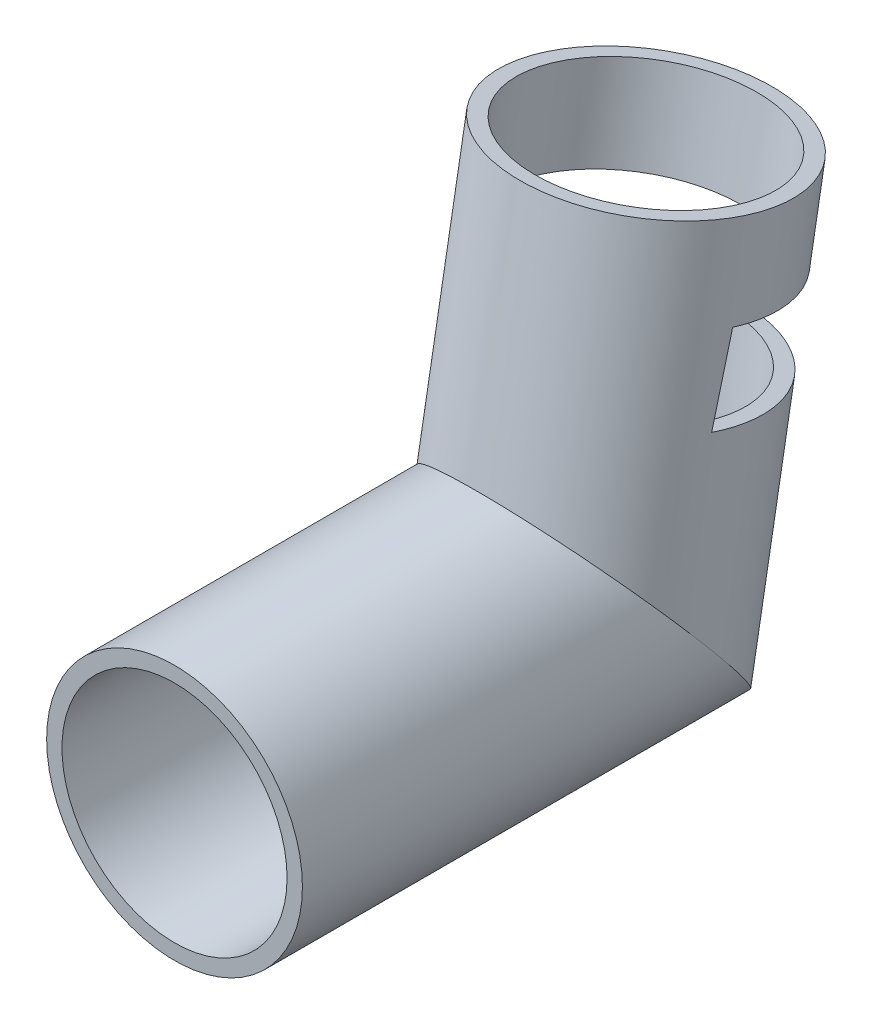
SolidWorks part; units mm, degrees
ref_plane "Front Plane" through (0, 0, 0) normal (0, 0, 1) x (1, 0, 0)
ref_plane "Top Plane" through (0, 0, 0) normal (0, 1, 0) x (1, 0, 0)
ref_plane "Right Plane" through (0, 0, 0) normal (1, 0, 0) x (0, 0, -1)
sketch "Sketch1" plane through (0, 0, 0) normal (1, 0, 0) x (0, 0, -1)
  line L0 (0, 0) -> (80, 0)
  line L1 (80, 0) -> (92.1554, 68.9365)
  line L2 (80, 0) -> (47.2364, 0) construction
  dimension "D1" = 80
sketch "Sketch3" plane through (0, 0, 0) normal (0, 0, 1) x (1, 0, 0)
  circle A0 centre (0, 0) radius 22
  circle A1 centre (0, 0) radius 25
sweep "Sweep1" add profiles "Sketch3" path "Sketch1"
sketch "Sketch4" plane through (0, 0, 0) normal (1, 0, 0) x (0, 0, -1)
  line L0 (80.6522, 36.2695) -> (50.0664, 10.6049)
  line L1 (100.9775, -25) -> (59.0225, 25) construction
  line L3 (100.9775, -25) -> (116.7756, 64.5953) construction
  line L4 (106.3111, 5.2485) -> (109.4487, 23.0428)
  line L7 (62.5438, 20.8034) -> (100.9775, -25)
  line L11 (113.6872, 47.0803) -> (109.4487, 23.0428)
  line L12 (80.6522, 36.2695) -> (110.8423, 30.9462)
  line L13 (80.6522, 36.2695) -> (84.5249, 52.2224)
  line L14 (113.6872, 47.0803) -> (94.7943, 50.4116)
  line L15 (94.7943, 50.4116) -> (84.5249, 52.2224)
extrude "Cut-Extrude2" cut sketch "Sketch4" against normal through all both and the other way through all
